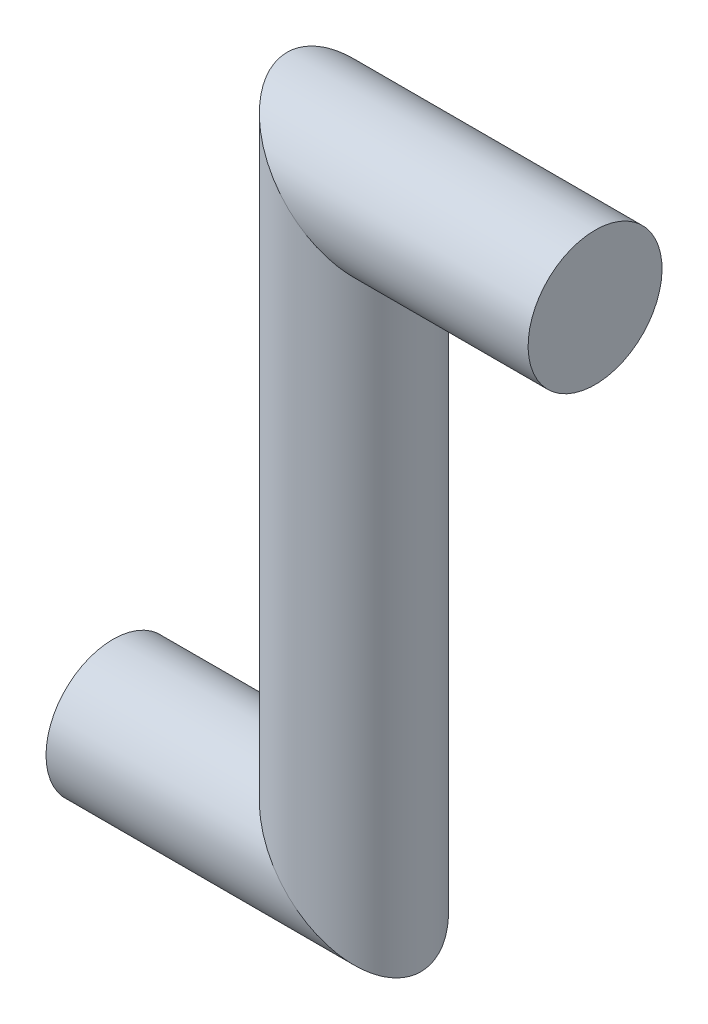
SolidWorks part; units mm, degrees
ref_plane "Alzado" through (0, 0, 0) normal (0, 0, 1) x (1, 0, 0)
ref_plane "Planta" through (0, 0, 0) normal (0, 1, 0) x (1, 0, 0)
ref_plane "Vista lateral" through (0, 0, 0) normal (1, 0, 0) x (0, 0, -1)
sketch "Croquis1" plane through (0, 0, 0) normal (0, 0, 1) x (1, 0, 0)
  line L8 (0, 0) -> (-18, 0)
  line L9 (-18, 0) -> (-18, -44.46)
  line L10 (-18, -44.46) -> (-36, -44.46)
  point P2 (0, 0)
  point P3 (0, 0)
  dimension "D1" = 18
  dimension "D2" = 18
  dimension "D3" = 44.46
sweep "Barrer1" add path "Croquis1" circular profile diameter 10 parameters "D3"=10
